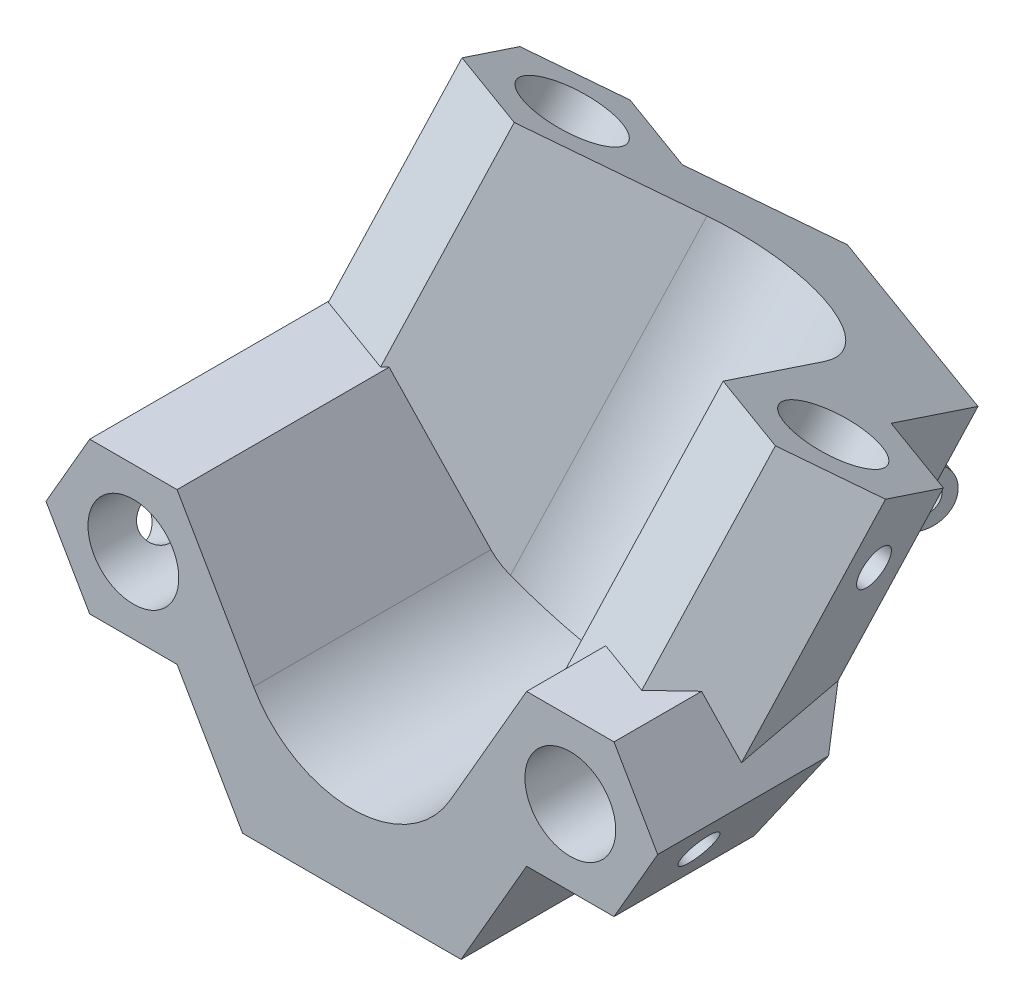
SolidWorks part; units mm, degrees
ref_plane "Front Plane" through (0, 0, 0) normal (0, 0, 1) x (1, 0, 0)
ref_plane "Top Plane" through (0, 0, 0) normal (0, 1, 0) x (1, 0, 0)
ref_plane "Right Plane" through (0, 0, 0) normal (1, 0, 0) x (0, 0, -1)
sketch "Sketch2" plane through (0, 0, 0) normal (0, 1, 0) x (1, 0, 0)
  line L0 (0, 0) -> (0, -10) construction
  line L1 (0, 0) -> (3.4202, 9.3969) construction
  dimension "D1" = 10
  dimension "D2" = 10
  dimension "D3" = 160
ref_plane "Plane1" through (0, 0, 0) normal (0.9397, 0, 0.342) x (0.342, 0, -0.9397)
sketch "Sketch3" plane through (0, 0, 0) normal (0.9397, 0, 0.342) x (0.342, 0, -0.9397)
  line L0 (0, 0) -> (10, 17.3205) construction
  line L1 (10, 17.3205) -> (10, 0) construction
  line L2 (10, 0) -> (0, 0) construction
  dimension "D1" = 30
  dimension "D2" = 10
sketch "Sketch5" plane through (0, 0, 0) normal (0, 0, 1) x (1, 0, 0)
  line L0 (0, 0) -> (10.3923, 0) construction
  line L1 (15.5205, 3.1177) -> (8.6603, 15)
  line L2 (8.6603, 15) -> (-8.6603, 15)
  line L3 (-8.6603, 15) -> (-13.8564, 6)
  line L4 (-13.8564, -6) -> (-8.6603, -15)
  line L5 (-8.6603, -15) -> (8.6603, -15)
  line L6 (8.6603, -15) -> (13.8564, -6)
  line L7 (0, -55) -> (0, 55) construction
  line L8 (24.2487, 0) -> (20.7846, 6)
  line L9 (20.7846, 6) -> (13.8564, 6)
  line L10 (13.8564, 6) -> (7.7942, -4.5)
  line L11 (10.3923, 0) -> (7.7942, 4.5) construction
  line L12 (13.8564, -6) -> (20.7846, -6)
  line L13 (20.7846, -6) -> (24.2487, 0)
  line L14 (-20.7846, -6) -> (-24.2487, 0)
  line L15 (-13.8564, -6) -> (-20.7846, -6)
  line L16 (-7.7942, 4.5) -> (-13.8564, -6) construction
  line L17 (-13.8564, 6) -> (-7.7942, -4.5)
  line L18 (-20.7846, 6) -> (-13.8564, 6)
  line L19 (-24.2487, 0) -> (-20.7846, 6)
  line L20 (-13.8564, 6) -> (-15.5205, 3.1177) construction
  line L21 (-15.5205, 3.1177) -> (-17.3205, 0) construction
  line L22 (-17.3205, 0) -> (-15.5205, -3.1177) construction
  line L23 (-15.5205, -3.1177) -> (-13.8564, -6) construction
  line L24 (-7.7942, -4.5) -> (-10.3923, 0) construction
  line L25 (-10.3923, 0) -> (-7.7942, 4.5) construction
  line L26 (12.1244, -3) -> (13.8564, -6) construction
  line L27 (13.8564, -6) -> (14.3205, -5.1962) construction
  line L28 (15.5205, -3.1177) -> (17.3205, 0) construction
  line L29 (14.3205, -5.1962) -> (15.5205, -3.1177) construction
  line L30 (7.7942, 4.5) -> (12.1244, -3) construction
  line L31 (7.7942, -4.5) -> (10.3923, 0) construction
  line L32 (10.3923, 0) -> (9, 0) construction
  line L33 (9, 0) -> (15, 0) construction
  line L34 (15, 0) -> (17.3205, 0) construction
  line L35 (17.3205, 0) -> (15.5205, 3.1177) construction
  circle A0 centre (0, 0) radius 15 construction
  arc A1 (-7.7942, -4.5) -> (7.7942, -4.5) centre (0, 0) ccw
  circle A2 centre (17.3205, 0) radius 6 construction
  circle A3 centre (17.3205, 0) radius 3.6
  circle A4 centre (-17.3205, 0) radius 3.6
  arc A5 (7.7942, -4.5) -> (-7.7942, -4.5) centre (0, 0) ccw construction
  dimension "D2" = 18
  dimension "D4" = 7.2
  dimension "D1" = 30
  dimension "D3" = 12
extrude "Boss-Extrude2" add sketch "Sketch5" along normal blind 15 contours A4 | L17 A1 L10 L9 L8 L13 L12 L6 L5 L4 L15 L14 L19 L18 | A3
ref_plane "Plane2" through (3.4202, 17.3205, -9.3969) normal (0.171, 0.866, -0.4698) x (0.9853, -0.1503, 0.0815)
sketch "Sketch10" plane through (0, 0, 0) normal (0, 0, -1) x (-1, 0, 0)
  line L0 (-7.7942, -4.5) -> (-13.8564, 6)
  line L1 (-13.8564, 6) -> (-20.7846, 6)
  line L2 (-20.7846, 6) -> (-24.2487, 0)
  line L3 (-24.2487, 0) -> (-20.7846, -6)
  line L4 (-20.7846, -6) -> (-13.8564, -6)
  line L5 (-13.8564, -6) -> (-8.6603, -15)
  line L6 (-8.6603, -15) -> (8.6603, -15)
  line L7 (8.6603, -15) -> (13.8564, -6)
  line L8 (13.8564, -6) -> (20.7846, -6)
  line L9 (20.7846, -6) -> (24.2487, 0)
  line L10 (24.2487, 0) -> (20.7846, 6)
  line L11 (20.7846, 6) -> (13.8564, 6)
  line L12 (20.7846, 6) -> (13.8564, 6) construction
  line L13 (13.8564, 6) -> (7.7942, -4.5)
  arc A0 (-7.7942, -4.5) -> (7.7942, -4.5) centre (0, 0) ccw
  arc A1 (-7.7942, -4.5) -> (7.7942, -4.5) centre (0, 0) ccw construction
  arc A2 (7.7942, -4.5) -> (-7.7942, -4.5) centre (0, 0) ccw construction
sketch "Sketch6" plane through (3.4202, 17.3205, -9.3969) normal (0.171, 0.866, -0.4698) x (0.9853, -0.1503, 0.0815)
  line L0 (-4.5094, -14.3061) -> (4.5094, 14.3061) construction
  line L1 (-3.7502, 16.9096) -> (-11.4117, 9.8881)
  line L2 (-15.7398, 1.6924) -> (-15.0192, -1.5568)
  line L3 (-12.769, -11.7026) -> (-4.5094, -14.3061) construction
  line L4 (11.4117, -9.8881) -> (12.096, -9.2609) construction
  line L5 (15.0192, 1.5568) -> (12.769, 11.7026)
  line L6 (12.769, 11.7026) -> (-3.7502, 16.9096)
  line L7 (2.6035, 8.2596) -> (0, 0) construction
  line L8 (-14.3061, 4.5094) -> (16.5193, -5.207) construction
  line L9 (3.7502, -16.9096) -> (11.4117, -9.8881) construction
  line L10 (23.127, -7.2898) -> (21.6269, -0.526)
  line L11 (21.6269, -0.526) -> (15.0192, 1.5568)
  line L12 (15.0192, 1.5568) -> (12.4654, -0.7837) construction
  line L13 (8.7865, 1.9487) -> (11.4117, -9.8881)
  line L14 (11.4117, -9.8881) -> (18.0194, -11.9709)
  line L15 (18.0194, -11.9709) -> (23.127, -7.2898)
  line L16 (-23.127, 7.2898) -> (-21.6269, 0.526)
  line L17 (-21.6269, 0.526) -> (-15.0192, -1.5568)
  line L18 (-15.0192, -1.5568) -> (-6.0809, 6.635)
  line L19 (-10.6616, 6.5061) -> (-11.4117, 9.8881) construction
  line L20 (-11.4117, 9.8881) -> (-18.0194, 11.9709)
  line L21 (-18.0194, 11.9709) -> (-23.127, 7.2898)
  line L22 (-4.5094, -14.3061) -> (3.7502, -16.9096) construction
  line L23 (-15.0192, -1.5568) -> (-12.769, -11.7026) construction
  line L24 (-6.0809, 6.635) -> (-9.9116, 3.1242) construction
  line L25 (-9.9116, 3.1242) -> (-8.7865, -1.9487) construction
  line L26 (-8.7865, -1.9487) -> (-10.6616, 6.5061) construction
  line L27 (-11.4117, 9.8881) -> (-12.096, 9.2609) construction
  line L28 (-13.8653, 7.6394) -> (-16.5193, 5.207) construction
  line L29 (-12.096, 9.2609) -> (-13.8653, 7.6394) construction
  line L30 (-16.5193, 5.207) -> (-14.3061, 4.5094) construction
  line L31 (-16.5193, 5.207) -> (-15.7398, 1.6924) construction
  line L32 (9.9116, -3.1242) -> (8.7865, 1.9487) construction
  line L33 (6.0809, -6.635) -> (9.9116, -3.1242) construction
  line L34 (12.4654, -0.7837) -> (6.0809, -6.635) construction
  line L35 (16.5193, -5.207) -> (15.7615, -1.79) construction
  line L36 (15.7615, -1.79) -> (15.2202, 0.6507) construction
  line L37 (15.2202, 0.6507) -> (15.0192, 1.5568) construction
  line L38 (13.939, -7.5718) -> (16.5193, -5.207) construction
  line L39 (12.096, -9.2609) -> (13.939, -7.5718) construction
  circle A0 centre (0, 0) radius 15 construction
  arc A1 (8.7865, 1.9487) -> (-6.0809, 6.635) centre (0, 0) ccw
  circle A2 centre (16.5193, -5.207) radius 6 construction
  circle A3 centre (16.5193, -5.207) radius 3.5
  circle A4 centre (-16.5193, 5.207) radius 6 construction
  circle A5 centre (-16.5193, 5.207) radius 3.6
  arc A6 (-2.7056, -8.5837) -> (8.7865, 1.9487) centre (0, 0) ccw construction
  arc A7 (-6.0809, 6.635) -> (-2.7056, -8.5837) centre (0, 0) ccw construction
  dimension "D2" = 18
  dimension "D3" = 7
  dimension "D5" = 7.2
  dimension "D1" = 30
  dimension "D4" = 12
  dimension "D6" = 12
extrude "Boss-Extrude3" add sketch "Sketch6" against normal up to surface (37.3205 mm away) contours L18 A1 L13 L14 L15 L10 L11 L5 L6 L1 L20 L21 L16 L17 | A5 | A3
sketch "Sketch7" plane through (0, 0, 15) normal (0, 0, 1) x (1, 0, 0)
  circle A0 centre (-17.3205, 0) radius 3.6
  circle A1 centre (-17.3205, 0) radius 3.6 construction
  circle A2 centre (0, 0) radius 9
  arc A3 (-7.7942, -4.5) -> (7.7942, -4.5) centre (0, 0) ccw construction
  circle A4 centre (17.3205, 0) radius 3.6
  arc A5 (17.0513, -3.5899) -> (15.6091, -3.1672) centre (17.3205, 0) ccw construction
extrude "Cut-Extrude1" cut sketch "Sketch7" against normal up to surface (15 mm away) up to face at (-10.5422, -2.7775, 0)
sketch "Sketch8" plane through (0, 0, 0) normal (0, 1, 0) x (1, 0, 0)
  line L0 (-24.2487, -15) -> (24.2487, -15)
  line L1 (24.2487, -15) -> (24.2487, -21.7571)
  line L2 (24.2487, -21.7571) -> (-24.2487, -21.7571)
  line L3 (-24.2487, -21.7571) -> (-24.2487, -15)
extrude "Cut-Extrude2" cut sketch "Sketch8" against normal through all both and the other way through all
sketch "Sketch9" plane through (0, 0, 15) normal (0, 0, 1) x (1, 0, 0)
  line L0 (-8.6603, -15) -> (-13.8564, -6)
  line L1 (-13.8564, -6) -> (-20.7846, -6)
  line L2 (-20.7846, -6) -> (-24.2487, 0)
  line L3 (-24.2487, 0) -> (-25.7483, -15)
  line L4 (-25.7483, -15) -> (-8.6603, -15)
  line L5 (8.6603, -15) -> (13.8564, -6)
  line L6 (13.8564, -6) -> (20.7846, -6)
  line L7 (20.7846, -6) -> (24.2487, 0)
  line L8 (24.2487, 0) -> (19.6596, -15)
  line L9 (19.6596, -15) -> (8.6603, -15)
extrude "Cut-Extrude3" cut sketch "Sketch9" against normal through all both and the other way through all
extrude "Boss-Extrude4" add sketch "Sketch10" along normal up to surface (12.8304 mm away)
sketch "Sketch11" plane through (3.4202, 17.3205, -9.3969) normal (0.171, 0.866, -0.4698) x (0.9853, -0.1503, 0.0815)
  line L0 (-3.7502, 16.9096) -> (-11.4117, 9.8881)
  line L1 (-11.4117, 9.8881) -> (-18.0194, 11.9709)
  line L2 (-18.0194, 11.9709) -> (-24.4549, 6.0728)
  line L3 (-22.6683, -13.1846) -> (-26.1144, 23.959) construction
  line L4 (-24.4549, 6.0728) -> (-26.1144, 23.959)
  line L5 (-26.1144, 23.959) -> (-3.7502, 16.9096)
  line L6 (12.769, 11.7026) -> (15.0192, 1.5568)
  line L7 (15.0192, 1.5568) -> (24.01, -1.2771)
  line L8 (25.1148, -13.1846) -> (23.1081, 8.4437) construction
  line L9 (24.01, -1.2771) -> (23.1081, 8.4437)
  line L10 (23.1081, 8.4437) -> (12.769, 11.7026)
extrude "Cut-Extrude4" cut sketch "Sketch11" against normal through all both and the other way through all
sketch "Sketch12" plane through (-18.1865, -10.5, 0) normal (-0.866, -0.5, 0) x (0, 0, 1)
  line L0 (15, 8.6603) -> (-7.4822, 8.6603) construction
  line L1 (15, 5.1962) -> (15, 12.1244) construction
  line L2 (-8.0554, 5.1962) -> (-6.909, 12.1244) construction
  circle A0 centre (10, 8.6603) radius 1.5
  dimension "D1" = 3
  dimension "D2" = 5
extrude "Cut-Extrude5" cut sketch "Sketch12" against normal up to surface and the other way through all up to face at (-20.9205, 0, 0)
sketch "Sketch13" plane through (18.1865, -10.5, 0) normal (0.866, -0.5, 0) x (0, 0, -1)
  line L0 (-15, 8.6603) -> (-2.6658, 8.6603) construction
  line L1 (-15, 5.1962) -> (-15, 12.1244) construction
  line L2 (-3.8786, 5.1962) -> (-1.453, 12.1244) construction
  circle A0 centre (-10, 8.6603) radius 1.5
  dimension "D1" = 3
  dimension "D2" = 5
extrude "Cut-Extrude6" cut sketch "Sketch13" against normal up to surface (2.7274 mm away) contours A0
sketch "Sketch14" plane through (20.1998, -5.25, -2.3247) normal (0.9619, -0.25, -0.1107) x (-0.1071, 0.0278, -0.9939)
  line L0 (1.8237, 21.7181) -> (-5.4703, 8.1224) construction
  line L1 (-1.2289, 23.3557) -> (4.8762, 20.0804) construction
  line L2 (-1.2869, 8.5925) -> (-9.6536, 7.6523) construction
  circle A0 centre (-0.5401, 17.3121) radius 1.5
  dimension "D1" = 3
  dimension "D2" = 5
extrude "Cut-Extrude7" cut sketch "Sketch14" against normal up to surface (2.5726 mm away)
sketch "Sketch15" plane through (-13.9797, -5.25, -14.765) normal (-0.6657, -0.25, -0.7031) x (-0.7462, 0.223, 0.6272)
  line L0 (3.8464, 21.4524) -> (9.4928, -2.5305) construction
  line L1 (0.4745, 20.6585) -> (7.2183, 22.2463) construction
  line L2 (9.1192, -2.9545) -> (13.7614, 2.3146) construction
  circle A0 centre (4.9923, 16.5855) radius 1.5
  dimension "D1" = 3
  dimension "D2" = 5
extrude "Cut-Extrude8" cut sketch "Sketch15" against normal up to surface (2.6593 mm away) contours A0
sketch "Sketch16" plane through (4.443, -7.5, -12.207) normal (0.2962, -0.5, -0.8138) x (-0.9551, -0.1551, -0.2524)
  line L0 (-3.5809, 19.6768) -> (1.5506, -8.5203) construction
  line L1 (-12.1012, 18.1262) -> (4.9394, 21.2274) construction
  line L2 (10.0709, -6.9697) -> (-4.4154, -9.606) construction
  line L3 (-3.7129, 6.4393) -> (-5.1453, 14.31)
  line L4 (-5.1453, 14.31) -> (-0.2261, 15.2052)
  line L5 (-0.2261, 15.2052) -> (1.2063, 7.3345)
  line L6 (1.2063, 7.3345) -> (-3.7129, 6.4393)
  point P8 (-2.6857, 14.7576)
  point P11 (0, 0)
  point P12 (0, 0)
  dimension "D1" = 5
  dimension "D2" = 8
  dimension "D3" = 5
extrude "Boss-Extrude5" add sketch "Sketch16" along normal blind 7
sketch "Sketch17" plane through (2.3492, 0, 0.8551) normal (0.9397, 0, 0.342) x (0.342, 0, -0.9397)
  line L0 (24.5526, -1.4737) -> (18.4904, 2.0263) construction
  line L3 (26.5526, 1.9904) -> (22.5526, -4.9378) construction
  line L4 (20.4904, 5.4904) -> (16.4904, -1.4378) construction
  circle A0 centre (22.3875, -0.2237) radius 1.25
  dimension "D1" = 2.5
  dimension "D2" = 2.5
extrude "Cut-Extrude9" cut sketch "Sketch17" against normal through all
sketch "Sketch18" plane through (2.3492, 0, 0.8551) normal (0.9397, 0, 0.342) x (0.342, 0, -0.9397)
  line L0 (20.3875, -3.6878) -> (24.3875, 3.2404) construction
  line L1 (22.5526, -4.9378) -> (16.4904, -1.4378) construction
  line L2 (26.5526, 1.9904) -> (20.4904, 5.4904) construction
  line L3 (20.4904, 5.4904) -> (23.5125, 1.7248)
  line L4 (20.4904, 5.4904) -> (26.5526, 1.9904)
  line L5 (26.5526, 1.9904) -> (22.5526, -4.9378)
  line L6 (22.5526, -4.9378) -> (16.4904, -1.4378)
  line L7 (16.4904, -1.4378) -> (21.2625, -2.1723)
  arc A0 (21.2625, -2.1723) -> (23.5125, 1.7248) centre (22.3875, -0.2237) ccw
  arc A1 (23.5125, 1.7248) -> (21.2625, -2.1723) centre (22.3875, -0.2237) ccw construction
  dimension "D1" = 4.5
extrude "Cut-Extrude10" cut sketch "Sketch18" against normal up to next
